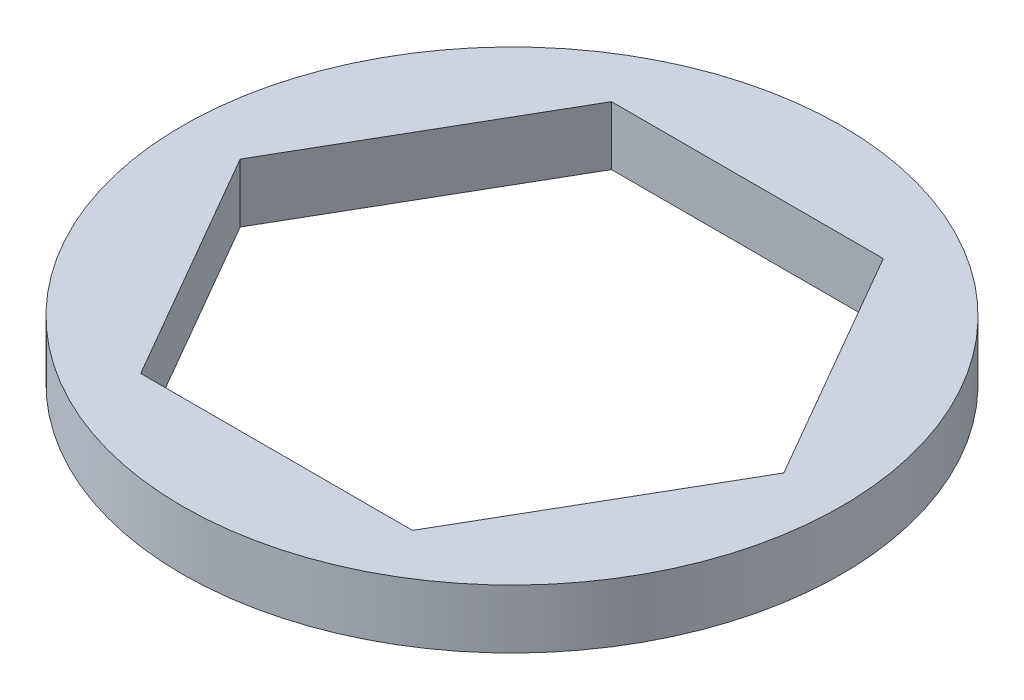
SolidWorks part; units mm, degrees
ref_plane "Front Plane" through (0, 0, 0) normal (0, 0, 1) x (1, 0, 0)
ref_plane "Top Plane" through (0, 0, 0) normal (0, 1, 0) x (1, 0, 0)
ref_plane "Right Plane" through (0, 0, 0) normal (1, 0, 0) x (0, 0, -1)
sketch "Sketch1" plane through (0, 0, 0) normal (0, 1, 0) x (1, 0, 0)
  line L1 (7.3323, 0) -> (3.6662, 6.35)
  line L2 (3.6662, 6.35) -> (-3.6662, 6.35)
  line L3 (-3.6662, 6.35) -> (-7.3323, 0)
  line L4 (-7.3323, 0) -> (-3.6662, -6.35)
  line L5 (-3.6662, -6.35) -> (3.6662, -6.35)
  line L6 (3.6662, -6.35) -> (7.3323, 0)
  circle A0 centre (0, 0) radius 6.35 construction
  circle A1 centre (0, 0) radius 8.89
  dimension "D1" = 12.7
  dimension "D3" = 17.78
  dimension "D2" = 6.35
extrude "Boss-Extrude1" add sketch "Sketch1" along normal blind 1.5875
